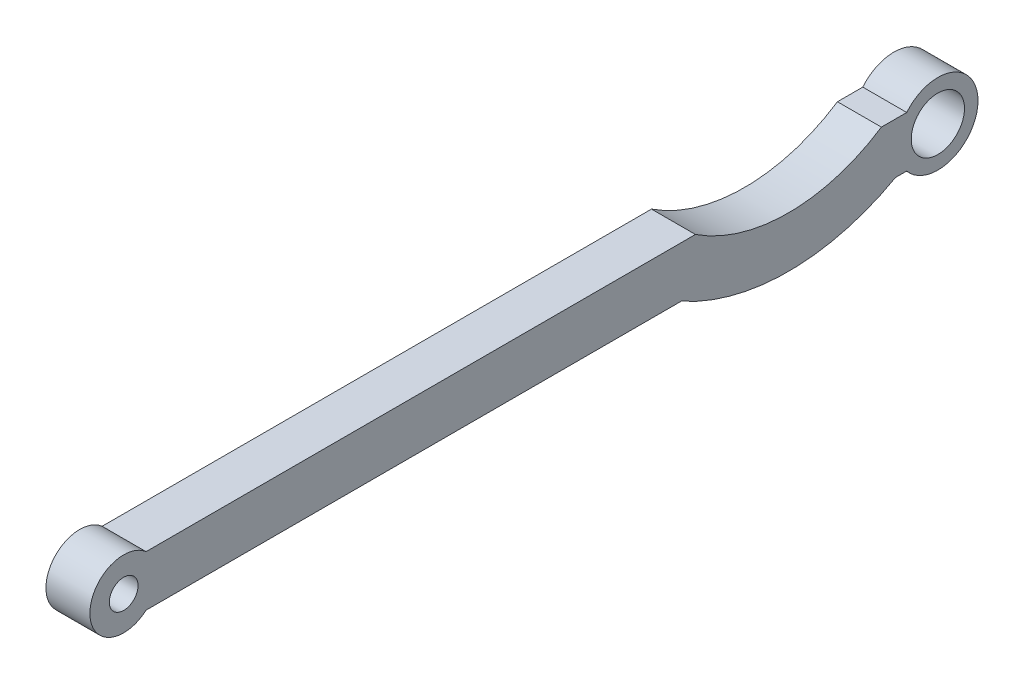
SolidWorks part; units mm, degrees
ref_plane "Спереди" through (0, 0, 0) normal (0, 0, 1) x (1, 0, 0)
ref_plane "Сверху" through (0, 0, 0) normal (0, 1, 0) x (1, 0, 0)
ref_plane "Справа" through (0, 0, 0) normal (1, 0, 0) x (0, 0, -1)
other "Configuration Table"
sketch "Эскиз1" plane through (0, 0, 0) normal (1, 0, 0) x (0, 0, -1)
  line L0 (35.2281, 3) -> (38.2281, 3)
  line L1 (-51.7719, 3) -> (13.2281, 3)
  line L3 (-51.7719, -3) -> (11.5569, -3)
  line L6 (38.2281, -3) -> (36.8994, -3)
  line L7 (41.9109, 0) -> (0, 0) construction
  arc A0 (35.2281, 3) -> (13.2281, 3) centre (24.2281, 19.7033) cw
  arc A2 (38.2281, -3) -> (38.2281, 3) centre (41.9109, 0) ccw
  circle A3 centre (41.9109, 0) radius 3.15
  arc A4 (-51.7719, 3) -> (-51.7719, -3) centre (-54.4176, 0) ccw
  circle A5 centre (-54.4176, 0) radius 1.7
  arc A6 (11.5569, -3) -> (36.8994, -3) centre (24.2281, 19.7033) ccw
  dimension "D3" = 20
  dimension "D4" = 26
  dimension "D5" = 9.5
  dimension "D7" = 6.3
  dimension "D10" = 8
  dimension "D11" = 3.4
  dimension "D1" = 6
  dimension "D2" = 90
  dimension "D6" = 3
  dimension "D9" = 22
extrude "Бобышка-Вытянуть1" add sketch "Эскиз1" along normal blind 5.2
